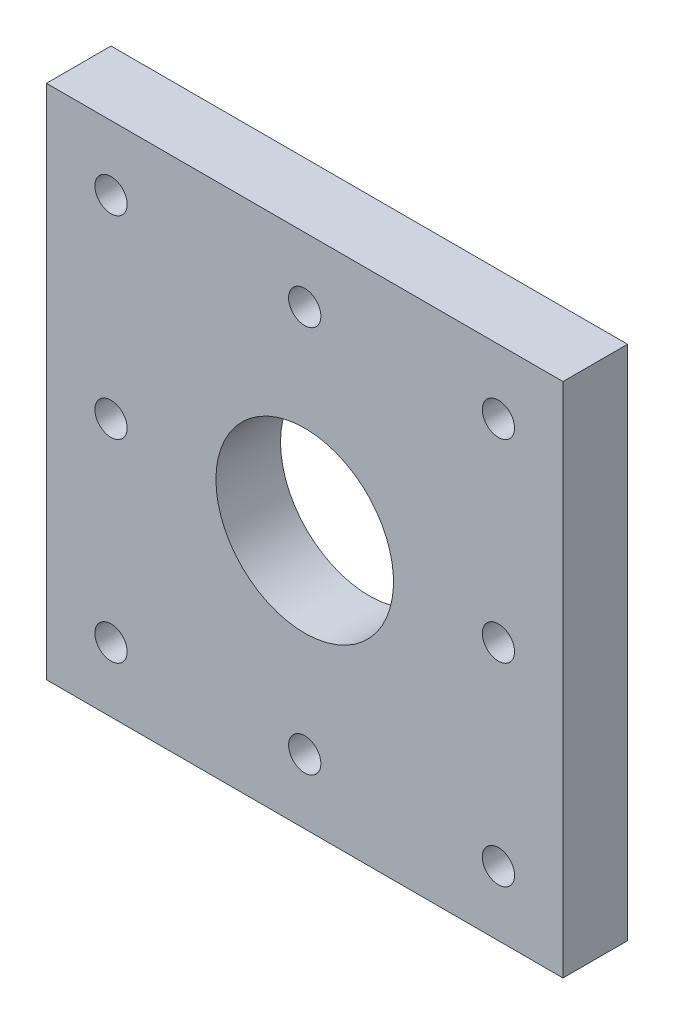
SolidWorks part; units mm, degrees
ref_plane "Front Plane" through (0, 0, 0) normal (0, 0, 1) x (1, 0, 0)
ref_plane "Top Plane" through (0, 0, 0) normal (0, 1, 0) x (1, 0, 0)
ref_plane "Right Plane" through (0, 0, 0) normal (1, 0, 0) x (0, 0, -1)
sketch "Sketch1" plane through (0, 0, 0) normal (0, 0, 1) x (1, 0, 0)
  line L1 (0, 0) -> (50.8, 0)
  line L2 (0, 0) -> (0, 50.8)
  line L3 (0, 50.8) -> (50.8, 50.8)
  line L4 (50.8, 0) -> (50.8, 50.8)
  dimension "D1" = 50.8
  dimension "D2" = 50.8
extrude "Boss-Extrude1" add sketch "Sketch1" along normal blind 6.35
sketch "Sketch2" plane through (0, 0, 0) normal (0, 0, -1) x (-1, 0, 0)
  line L0 (0, 25.4) -> (-50.8, 25.4) construction
  line L1 (0, 50.8) -> (0, 0) construction
  line L2 (-50.8, 0) -> (-50.8, 50.8) construction
  line L3 (-25.4, 50.8) -> (-25.4, 0) construction
  line L4 (-50.8, 50.8) -> (0, 50.8) construction
  line L5 (0, 0) -> (-50.8, 0) construction
  circle A0 centre (-25.4, 25.4) radius 8.7313
  dimension "D1" = 17.4625
sketch "Sketch4" plane through (0, 0, 0) normal (0, 0, -1) x (-1, 0, 0)
  line L0 (-25.4, 50.8) -> (-25.4, 0) construction
  line L1 (-50.8, 50.8) -> (0, 50.8) construction
  line L2 (0, 0) -> (-50.8, 0) construction
  line L3 (-50.8, 25.4) -> (0, 25.4) construction
  line L4 (-50.8, 0) -> (-50.8, 50.8) construction
  line L5 (0, 50.8) -> (0, 0) construction
ref_plane "Plane1" through (25.4, 0, 0) normal (1, 0, 0) x (0, -1, 0)
ref_plane "Plane2" through (0, 25.4, 0) normal (0, -1, 0) x (-1, 0, 0)
extrude "Cut-Extrude7" cut sketch "Sketch2" against normal through all contours A0
sketch "Sketch5" plane through (0, 0, 6.35) normal (0, 0, 1) x (1, 0, 0)
  line L0 (25.4, 0) -> (25.4, 6.35) construction
  line L1 (0, 0) -> (50.8, 0) construction
  line L2 (50.8, 25.4) -> (44.45, 25.4) construction
  line L3 (50.8, 0) -> (50.8, 50.8) construction
  line L4 (25.4, 50.8) -> (25.4, 44.45) construction
  line L5 (50.8, 50.8) -> (0, 50.8) construction
  line L6 (0, 25.4) -> (6.35, 25.4) construction
  line L7 (0, 50.8) -> (0, 0) construction
  circle A0 centre (25.4, 6.35) radius 1.5875
  circle A1 centre (6.35, 25.4) radius 1.5875
  circle A2 centre (25.4, 44.45) radius 1.5875
  circle A3 centre (44.45, 25.4) radius 1.5875
  dimension "D1" = 3.175
  dimension "D4" = 3.175
  dimension "D6" = 3.175
  dimension "D7" = 3.175
  dimension "D2" = 6.35
  dimension "D3" = 6.35
  dimension "D5" = 6.35
  dimension "D8" = 6.35
extrude "Cut-Extrude8" cut sketch "Sketch5" against normal through all
sketch "Sketch7" plane through (0, 0, 0) normal (0, 0, -1) x (-1, 0, 0)
  circle A0 centre (-6.35, 6.35) radius 1.5875
  circle A1 centre (-44.45, 6.35) radius 1.5875
  circle A2 centre (-44.45, 44.45) radius 1.5875
  circle A3 centre (-6.35, 44.45) radius 1.5875
  dimension "D1" = 3.175
  dimension "D2" = 3.175
  dimension "D3" = 3.175
  dimension "D4" = 3.175
extrude "Cut-Extrude9" cut sketch "Sketch7" against normal through all
equation "\"dist\"= 10"
